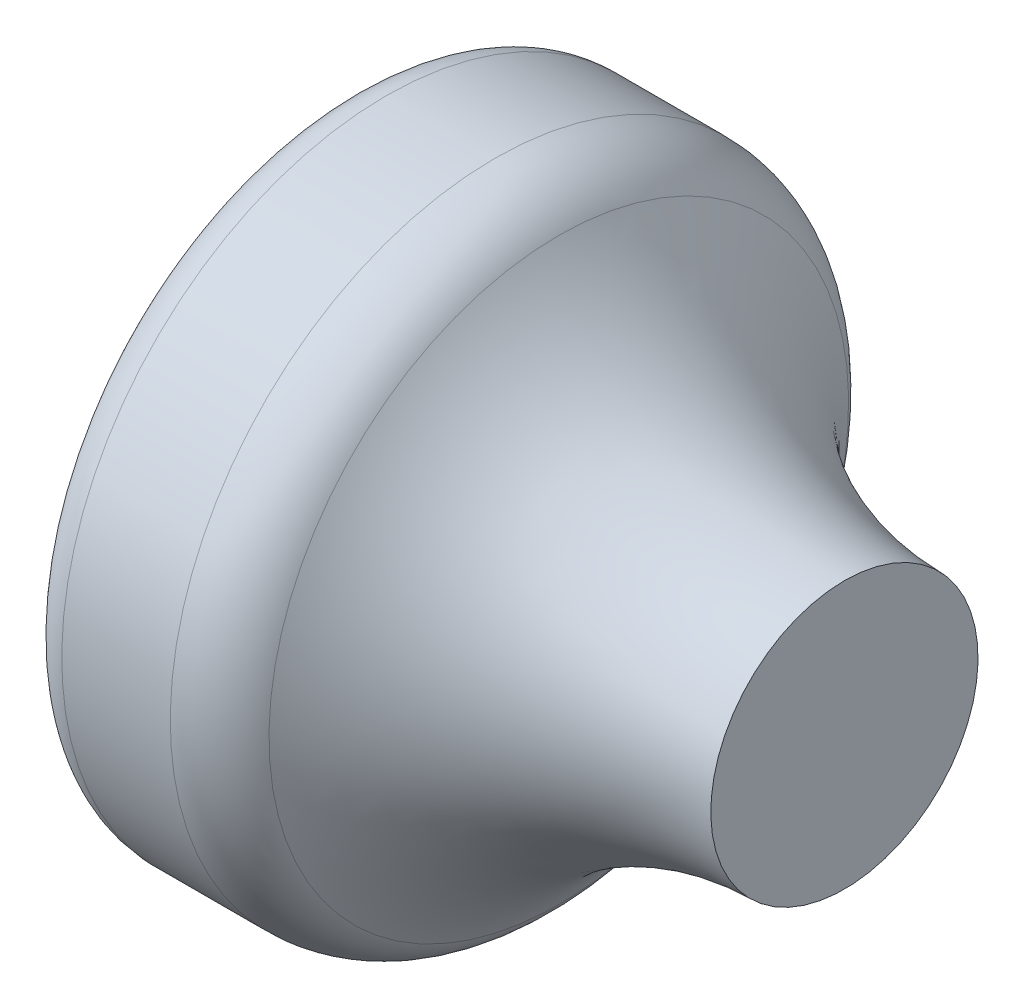
SolidWorks part; units mm, degrees
ref_plane "Front Plane" through (0, 0, 0) normal (0, 0, 1) x (1, 0, 0)
ref_plane "Top Plane" through (0, 0, 0) normal (0, 1, 0) x (1, 0, 0)
ref_plane "Right Plane" through (0, 0, 0) normal (1, 0, 0) x (0, 0, -1)
sketch "Sketch1" plane through (0, 0, 0) normal (0, 0, 1) x (1, 0, 0)
  line L0 (-13, 0) -> (-13, 7.5)
  line L1 (-12, 8.5) -> (-9.1573, 8.5)
  line L3 (0, 3.5) -> (0, 0)
  line L4 (0, 0) -> (-13, 0)
  arc A0 (0, 3.5) -> (-7.481, 7.5909) centre (0.0624, 12.4998) cw
  arc A1 (-13, 7.5) -> (-12, 8.5) centre (-12, 7.5) cw
  arc A2 (-9.1573, 8.5) -> (-7.481, 7.5909) centre (-9.1573, 6.5) cw
  point P8 (-13, 8.5)
  point P11 (-8, 8.5)
  dimension "D5" = 1
  dimension "D6" = 2
  dimension "D7" = 9
  dimension "D1" = 3.5
  dimension "D2" = 8.5
  dimension "D3" = 13
  dimension "D4" = 5
  dimension "D8" = 0
revolve "Revolve1" add sketch "Sketch1" angle 360 about L4
